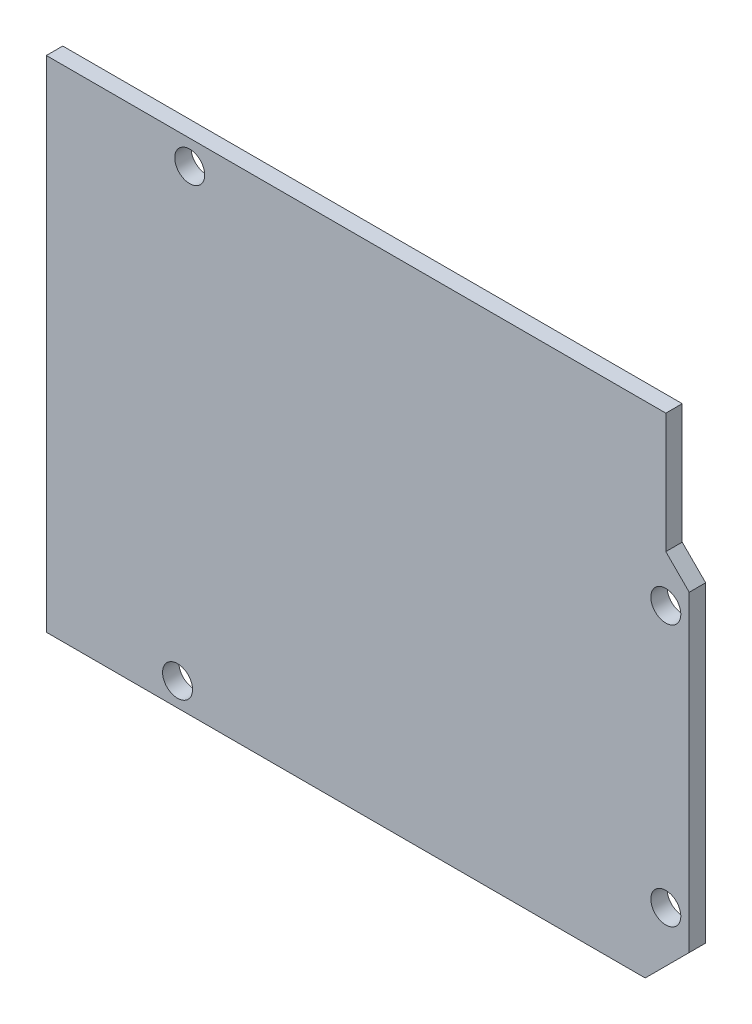
SolidWorks part; units mm, degrees
ref_plane "Front Plane" through (0, 0, 0) normal (0, 0, 1) x (1, 0, 0)
ref_plane "Top Plane" through (0, 0, 0) normal (0, 1, 0) x (1, 0, 0)
ref_plane "Right Plane" through (0, 0, 0) normal (1, 0, 0) x (0, 0, -1)
sketch "Sketch1" plane through (0, 0, 0) normal (0, 0, 1) x (1, 0, 0)
  line L1 (-34.3, -26.65) -> (34.3, -26.65)
  line L2 (-34.3, -26.65) -> (-34.3, 26.65)
  line L3 (-34.3, 26.65) -> (34.3, 26.65)
  line L4 (34.3, -26.65) -> (34.3, 26.65)
  line L5 (-34.3, -26.65) -> (34.3, 26.65) construction
  line L6 (-34.3, 26.65) -> (34.3, -26.65) construction
  point P0 (0, 0)
  dimension "D1" = 68.6
  dimension "D2" = 53.3
extrude "Boss-Extrude1" add sketch "Sketch1" along normal blind 1.75
sketch "Sketch2" plane through (0, 0, 1.75) normal (0, 0, 1) x (1, 0, 0)
  line L2 (-34.3, 26.65) -> (-34.3, -26.65) construction
  line L3 (-34.3, -26.65) -> (34.3, -26.65) construction
  circle A0 centre (-19, 24.05) radius 1.6
  circle A1 centre (-20.3, -24.15) radius 1.6
  circle A2 centre (31.8, 8.85) radius 1.6
  circle A3 centre (31.8, -19.05) radius 1.6
  dimension "D2" = 14
  dimension "D7" = 3.2
  dimension "D1" = 15.3
  dimension "D3" = 2.5
  dimension "D4" = 5.1
  dimension "D5" = 27.9
  dimension "D6" = 15.2
  dimension "D8" = 50.8
sketch "Sketch3" plane through (0, 0, 1.75) normal (0, 0, 1) x (1, 0, 0)
  line L0 (31.8, 26.65) -> (31.8, 13.85)
  line L1 (34.3, 26.65) -> (-34.3, 26.65) construction
  line L2 (31.8, 13.85) -> (50.9499, -5.2999)
  line L4 (50.9499, -5.2999) -> (28.345, -27.9048)
  line L5 (28.345, -27.9048) -> (59.3089, -27.9048)
  line L6 (59.3089, -27.9048) -> (59.3089, 26.65)
  line L7 (59.3089, 26.65) -> (31.8, 26.65)
  dimension "D1" = 135
  dimension "D2" = 5
extrude "Cut-Extrude1" cut sketch "Sketch2" against normal through all
extrude "Cut-Extrude2" cut sketch "Sketch3" against normal through all
